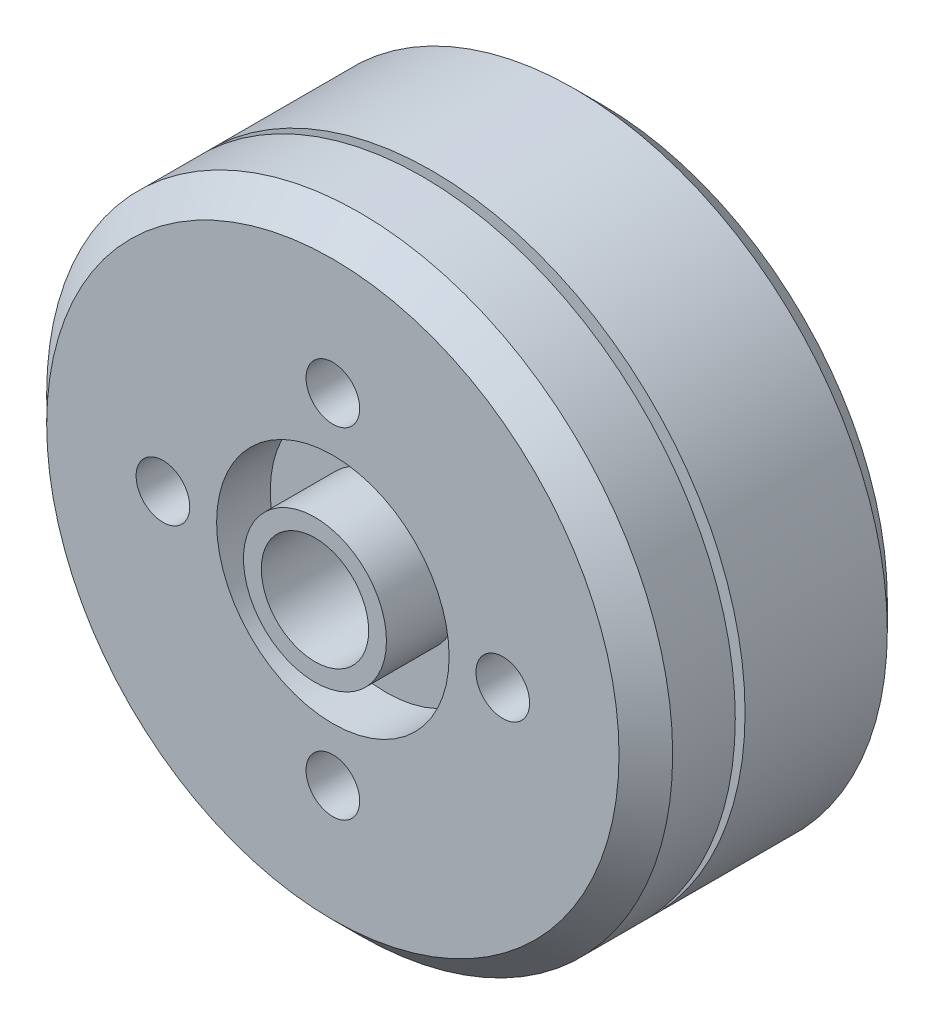
SolidWorks part; units mm, degrees
ref_plane "前视基准面" through (0, 0, 0) normal (0, 0, 1) x (1, 0, 0)
ref_plane "上视基准面" through (0, 0, 0) normal (0, 1, 0) x (1, 0, 0)
ref_plane "右视基准面" through (0, 0, 0) normal (1, 0, 0) x (0, 0, -1)
sketch "草图1" plane through (0, 0, 0) normal (0, 0, 1) x (1, 0, 0)
  circle A0 centre (0, 0) radius 17.5
extrude "凸台-拉伸1" add sketch "草图1" along normal blind 15
sketch "草图2" plane through (0, 0, 0) normal (0, 0, -1) x (-1, 0, 0)
  circle A0 centre (0, -8) radius 1.5
  circle A1 centre (-8, 0) radius 1.5
  circle A2 centre (0, 8) radius 1.5
  circle A3 centre (8, 0) radius 1.5
  point P12 (0, 0)
  dimension "D1" = 4
extrude "切除-拉伸1" cut sketch "草图2" against normal blind 5
sketch "草图3" plane through (0, 0, 0) normal (0, 1, 0) x (1, 0, 0)
  line L2 (13.2844, -9.9531) -> (13.2844, -10)
  line L12 (0, 0) -> (0, -15)
  line L13 (-17.5, -15) -> (17.5, -15) construction
  line L16 (13.2844, -9.9531) -> (13.2844, -9.4531)
  line L17 (13.2844, -9.4531) -> (17.9693, -9.4531)
  line L18 (17.9693, -10) -> (17.9693, -9.4531)
  line L19 (17.9693, -10) -> (13.2844, -10)
revolve "切除-旋转1" cut sketch "草图3" angle 360 about L12
sketch "草图4" plane through (0, 0, 0) normal (0, 0, -1) x (-1, 0, 0)
  circle A0 centre (0, 0) radius 3
extrude "切除-拉伸2" cut sketch "草图4" against normal blind 20
sketch "草图5" plane through (0, 0, 15) normal (0, 0, 1) x (1, 0, 0)
  circle A0 centre (0, -9.5) radius 1.5
  circle A1 centre (-9.5, 0) radius 1.5
  circle A2 centre (0, 9.5) radius 1.5
  circle A3 centre (9.5, 0) radius 1.5
  point P12 (0, 0)
  dimension "D1" = 4
extrude "切除-拉伸3" cut sketch "草图5" against normal blind 6
chamfer "倒角1" distance 1.5 angle 45 2 edges at (17.5, 0, 15) (17.5, 0, 0)
sketch "草图6" plane through (0, 0, 15) normal (0, 0, 1) x (1, 0, 0)
  circle A0 centre (0, 0) radius 6.5
  circle A1 centre (0, 0) radius 3.9966
extrude "切除-拉伸4" cut sketch "草图6" against normal blind 3
sketch "草图7" plane through (0, 0, 15) normal (0, 0, 1) x (1, 0, 0)
  circle A0 centre (0, 0) radius 3
  circle A1 centre (0, 0) radius 3.9966
extrude "凸台-拉伸2" add sketch "草图7" along normal blind 1
